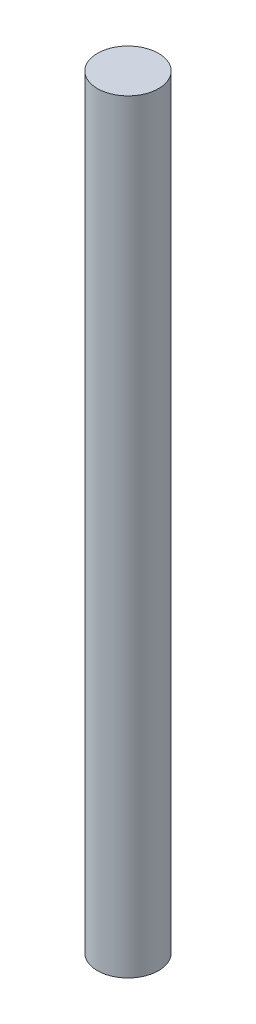
SolidWorks part; units mm, degrees
ref_plane "Front Plane" through (0, 0, 0) normal (0, 0, 1) x (1, 0, 0)
ref_plane "Top Plane" through (0, 0, 0) normal (0, 1, 0) x (1, 0, 0)
ref_plane "Right Plane" through (0, 0, 0) normal (1, 0, 0) x (0, 0, -1)
sketch "Sketch1" plane through (0, 0, 0) normal (0, 1, 0) x (1, 0, 0)
  circle A0 centre (0, 0) radius 4
extrude "Boss-Extrude1" add sketch "Sketch1" along normal blind 100
